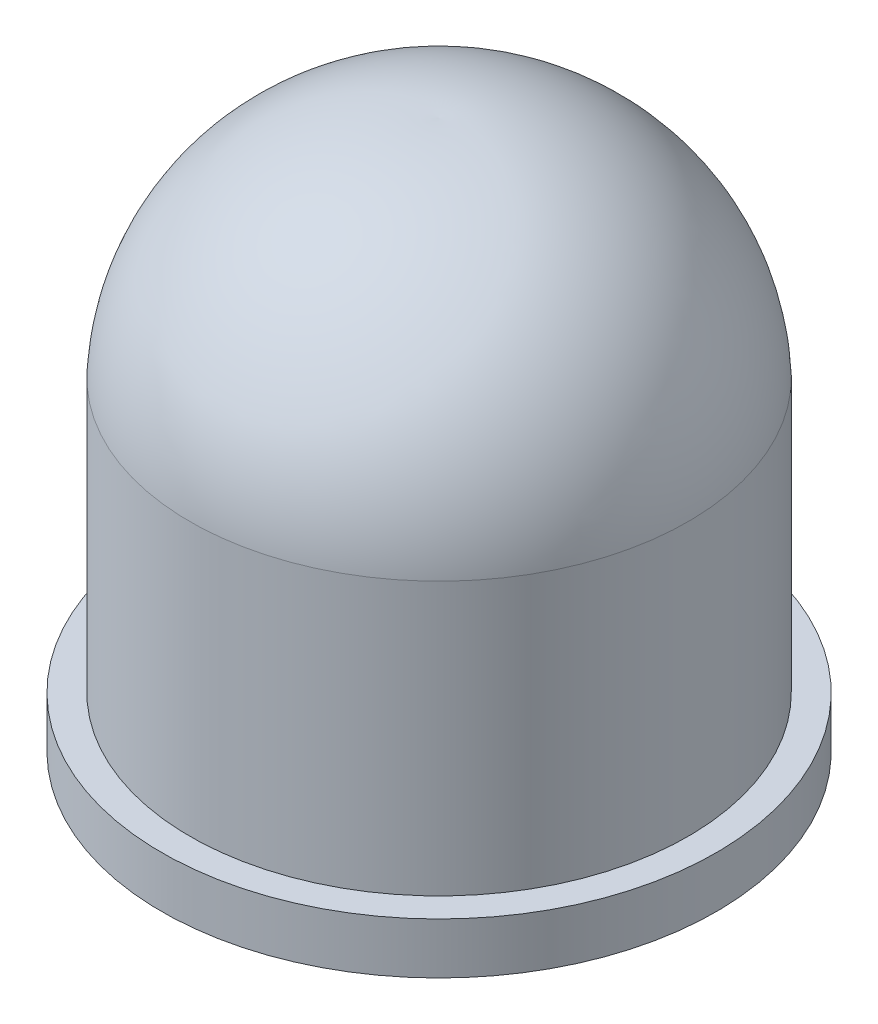
SolidWorks part; units mm, degrees
ref_plane "Front Plane" through (0, 0, 0) normal (0, 0, 1) x (1, 0, 0)
ref_plane "Top Plane" through (0, 0, 0) normal (0, 1, 0) x (1, 0, 0)
ref_plane "Right Plane" through (0, 0, 0) normal (1, 0, 0) x (0, 0, -1)
sketch "Sketch1" plane through (0, 0, 0) normal (0, 0, 1) x (1, 0, 0)
  line L0 (0, 0) -> (0, 5.841)
  line L1 (0, 0) -> (2.95, 0)
  line L2 (2.95, 0) -> (2.95, 0.5437)
  line L3 (2.95, 0.5437) -> (2.65, 0.5437)
  line L4 (2.65, 0.5437) -> (2.65, 3.4437)
  arc A0 (0, 5.841) -> (2.65, 3.4437) centre (0.1263, 3.3173) cw
revolve "Revolve3" add sketch "Sketch1" angle 360 about L0
